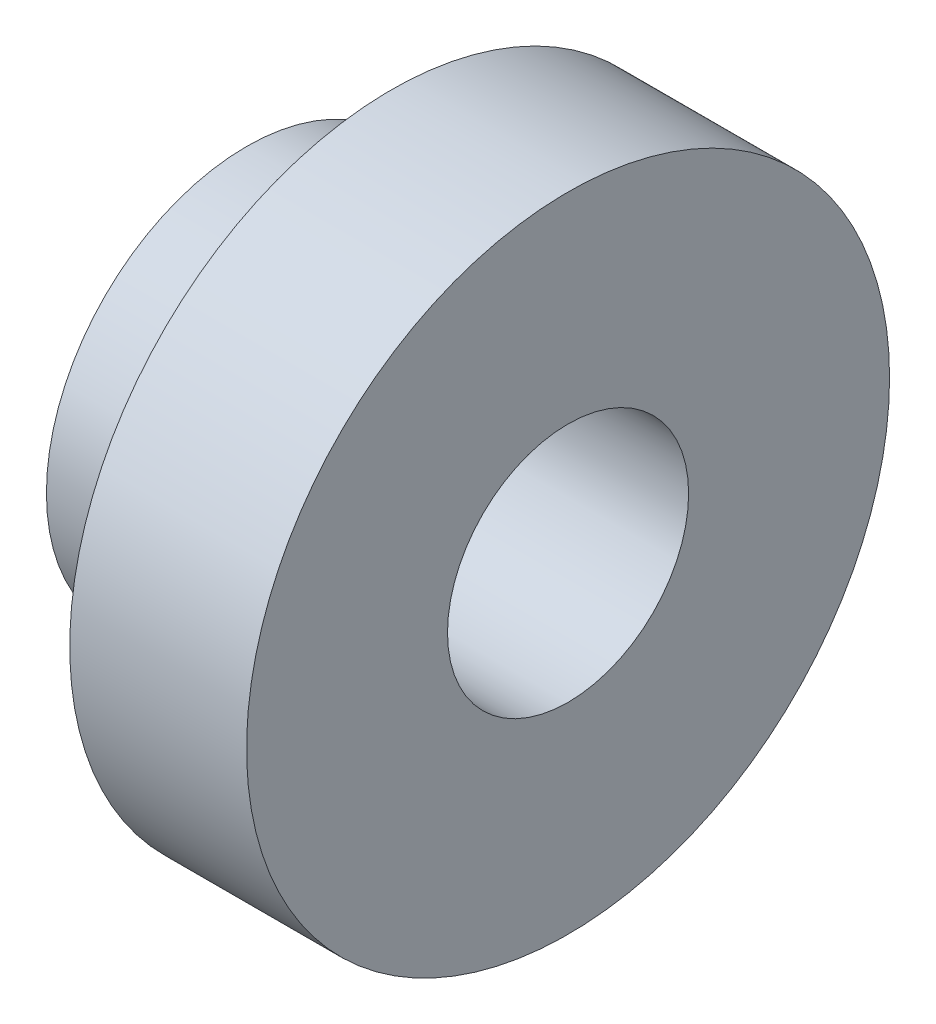
SolidWorks part; units mm, degrees
material "Laiton"
ref_plane "Plan de face" through (0, 0, 0) normal (0, 0, 1) x (1, 0, 0)
ref_plane "Plan de dessus" through (0, 0, 0) normal (0, 1, 0) x (1, 0, 0)
ref_plane "Plan de droite" through (0, 0, 0) normal (1, 0, 0) x (0, 0, -1)
sketch "Esquisse1" plane through (0, 0, 0) normal (0, 0, 1) x (1, 0, 0)
  line L0 (0, 0) -> (0, 1.5)
  line L1 (0, 1.5) -> (-4, 1.5)
  line L2 (-4, 1.5) -> (-4, 2.49)
  line L3 (-4, 2.49) -> (-2.2, 2.49)
  line L4 (-2.2, 2.49) -> (-2.2, 4)
  line L5 (-2.2, 4) -> (0, 4)
  line L6 (0, 4) -> (0, 1.5)
  line L7 (0, 0) -> (-50.8277, 0) construction
  dimension "D1" = 3
  dimension "D2" = 8
  dimension "D3" = 4.98
  dimension "D4" = 1.8
  dimension "D5" = 4
revolve "Révolution1" add sketch "Esquisse1" angle 360 about L7
